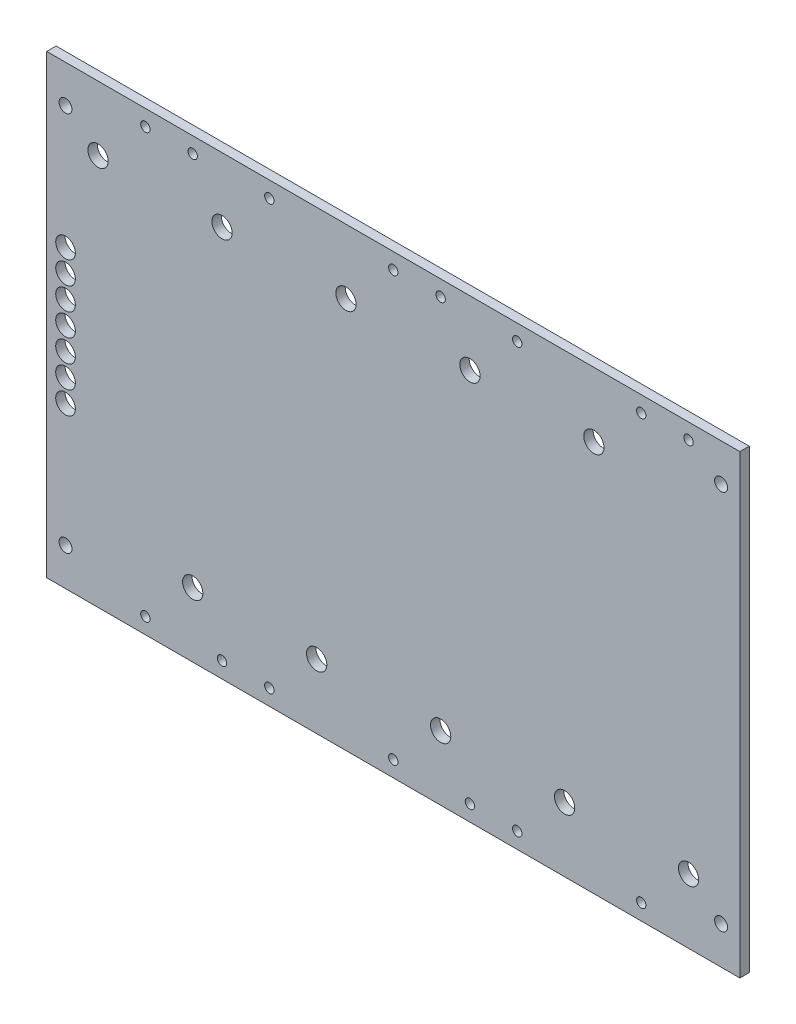
SolidWorks part; units mm, degrees
ref_plane "Front Plane" through (0, 0, 0) normal (0, 0, 1) x (1, 0, 0)
ref_plane "Top Plane" through (0, 0, 0) normal (0, 1, 0) x (1, 0, 0)
ref_plane "Right Plane" through (0, 0, 0) normal (1, 0, 0) x (0, 0, -1)
sketch "Sketch1" plane through (0, 0, 0) normal (0, 0, 1) x (1, 0, 0)
  line L0 (20.955, 77.0636) -> (20.955, 0) construction
  line L1 (0, 0) -> (110.8202, 0)
  line L2 (0, 0) -> (0, 77.0636) construction
  line L3 (0, 77.0636) -> (110.8202, 77.0636)
  line L4 (110.8202, 77.0636) -> (110.8202, 0)
  line L5 (20.6502, 77.0636) -> (20.6502, 0) construction
  line L6 (10.3251, 74.3712) -> (0, 74.3712) construction
  line L7 (10.3251, 74.3712) -> (20.6502, 74.3712) construction
  line L8 (10.3251, 2.6924) -> (10.3251, 0) construction
  line L9 (10.3251, 74.3712) -> (10.3251, 77.0636) construction
  line L10 (18.3261, 66.1543) -> (20.6502, 66.1543) construction
  line L11 (2.3241, 66.1543) -> (0, 66.1543) construction
  line L12 (18.3261, 10.9093) -> (20.6502, 10.9093) construction
  line L13 (41.6052, 77.0636) -> (41.6052, 0) construction
  line L14 (18.3261, 66.1543) -> (18.3261, 77.0636) construction
  line L15 (18.3261, 10.9093) -> (18.3261, 0) construction
  line L16 (20.955, 66.1543) -> (23.2791, 66.1543) construction
  line L17 (41.6052, 66.1543) -> (36.2579, 66.1543) construction
  line L18 (41.6052, 74.3712) -> (20.955, 74.3712) construction
  line L19 (31.2801, 74.3712) -> (31.2801, 77.0636) construction
  line L20 (31.2801, 0) -> (31.2801, 2.6924) construction
  line L21 (0, 77.0636) -> (-6.35, 77.0636)
  line L22 (-6.35, 77.0636) -> (-6.35, 0)
  line L23 (-6.35, 0) -> (0, 0)
  line L24 (41.6052, 10.9093) -> (39.2811, 10.9093) construction
  line L25 (41.6052, 2.6924) -> (31.2801, 2.6924) construction
  line L26 (83.5152, 77.0636) -> (83.5152, 0) construction
  line L27 (-3.175, 70.7136) -> (-3.175, 77.0636) construction
  line L28 (-3.175, 6.35) -> (-3.175, 0) construction
  line L29 (62.865, 77.0636) -> (62.865, 0) construction
  line L30 (62.5602, 77.0636) -> (62.5602, 0) construction
  line L31 (41.91, 0) -> (41.91, 77.0636) construction
  line L34 (104.4702, 77.0636) -> (104.4702, 0) construction
  line L35 (83.82, 0) -> (83.82, 77.0636) construction
  line L36 (41.6052, 77.0636) -> (83.5152, 77.0636) construction
  line L37 (107.6452, 77.0636) -> (107.6452, 70.7136) construction
  line L38 (107.6452, 0) -> (107.6452, 6.35) construction
  line L39 (20.955, 2.6924) -> (23.2791, 2.6924) construction
  line L40 (23.2791, 2.6924) -> (65.1891, 2.6924) construction
  line L42 (-3.175, 38.5318) -> (-6.35, 38.5318) construction
  line L43 (-3.175, 38.5318) -> (-3.175, 42.3418) construction
  line L44 (104.775, 77.0636) -> (104.775, 0) construction
  line L45 (125.4252, 77.0636) -> (125.4252, 0) construction
  circle A0 centre (10.3251, 74.3712) radius 0.7937
  circle A1 centre (10.3251, 2.6924) radius 0.7937
  circle A2 centre (2.3241, 66.1543) radius 1.7145
  circle A3 centre (18.3261, 74.4347) radius 0.7937
  circle A4 centre (18.3261, 10.9093) radius 1.7145
  circle A5 centre (23.2791, 66.1543) radius 1.7145
  circle A6 centre (31.2801, 74.3712) radius 0.7937
  circle A7 centre (31.2801, 2.6924) radius 0.7937
  circle A8 centre (39.2811, 10.9093) radius 1.7145
  circle A9 centre (31.2801, 2.6924) radius 0.7937
  circle A10 centre (65.1891, 66.1543) radius 1.7145
  circle A11 centre (73.1901, 2.6924) radius 0.7937
  circle A12 centre (73.1901, 2.6924) radius 0.7937
  circle A13 centre (81.1911, 10.9093) radius 1.7145
  circle A14 centre (73.1901, 74.3712) radius 0.7937
  circle A15 centre (65.1891, 2.6924) radius 0.7937
  circle A16 centre (52.2351, 74.3712) radius 0.7937
  circle A17 centre (44.2341, 66.1543) radius 1.7145
  circle A18 centre (-3.175, 70.7136) radius 1.0922
  circle A19 centre (-3.175, 6.35) radius 1.0922
  circle A20 centre (60.2361, 10.9093) radius 1.7145
  circle A21 centre (52.2351, 2.6924) radius 0.7937
  circle A26 centre (60.2361, 74.4347) radius 0.7937
  circle A27 centre (102.1461, 74.4347) radius 0.7937
  circle A28 centre (94.1451, 74.3712) radius 0.7937
  circle A29 centre (86.1441, 66.1543) radius 1.7145
  circle A30 centre (102.1461, 10.9093) radius 1.7145
  circle A31 centre (94.1451, 2.6924) radius 0.7937
  circle A32 centre (107.6452, 70.7136) radius 1.0922
  circle A33 centre (107.6452, 6.35) radius 1.0922
  circle A34 centre (23.2791, 2.6924) radius 0.7937
  circle A35 centre (60.2361, 74.4347) radius 0.7937 [skipped]
  circle A36 centre (115.1001, 74.3712) radius 0.7937 [skipped]
  circle A38 centre (102.1461, 74.4347) radius 0.7937
  circle A40 centre (-3.175, 38.5318) radius 1.6593
  circle A41 centre (-3.175, 42.3418) radius 1.6593
  circle A42 centre (-3.175, 46.1518) radius 1.6593
  circle A43 centre (-3.175, 49.9618) radius 1.6593
  circle A44 centre (-3.175, 38.5318) radius 1.6593
  circle A45 centre (-3.175, 42.3418) radius 1.6593
  circle A46 centre (-3.175, 46.1518) radius 1.6593
  circle A47 centre (-3.175, 34.7218) radius 1.6593
  circle A48 centre (-3.175, 38.5318) radius 1.6593
  circle A49 centre (-3.175, 42.3418) radius 1.6593
  circle A50 centre (-3.175, 30.9118) radius 1.6593
  circle A51 centre (-3.175, 34.7218) radius 1.6593
  circle A52 centre (-3.175, 38.5318) radius 1.6593
  circle A53 centre (-3.175, 34.7218) radius 1.6593
  circle A54 centre (-3.175, 30.9118) radius 1.6593
  circle A55 centre (-3.175, 27.1018) radius 1.6593
  circle A56 centre (123.1011, 10.9093) radius 1.7145 [skipped]
  circle A57 centre (115.1001, 2.6924) radius 0.7937 [skipped]
  circle A58 centre (107.0991, 2.6924) radius 0.7937 [skipped]
  circle A59 centre (107.0991, 66.1543) radius 1.7145 [skipped]
  circle A60 centre (115.1001, 2.6924) radius 0.7937 [skipped]
  dimension "D6" = 1.5875
  dimension "D7" = 3.429
  dimension "D13" = 2.1844
  dimension "D15" = 20.6502
  dimension "D11" = 1.5875
  dimension "D16" = 3
  dimension "D18" = 41.91
  dimension "D24" = 3.3186
  dimension "D1" = 77.0636
  dimension "D3" = 20.6502
  dimension "D4" = 20.955
  dimension "D5" = 71.6788
  dimension "D8" = 16.002
  dimension "D9" = 55.245
  dimension "D10" = 8.2804
  dimension "D12" = 6.35
  dimension "D14" = 6.35
  dimension "D17" = 3
  dimension "D19" = 71.6788
  dimension "D20" = 3.175
  dimension "D21" = 41.91
  dimension "D23" = 117.1702
  dimension "D27" = 3.81
  dimension "D22" = 6.35
  dimension "D25" = 4
  dimension "D26" = 4
extrude "Boss-Extrude1" add sketch "Sketch1" along normal blind 1.5875
